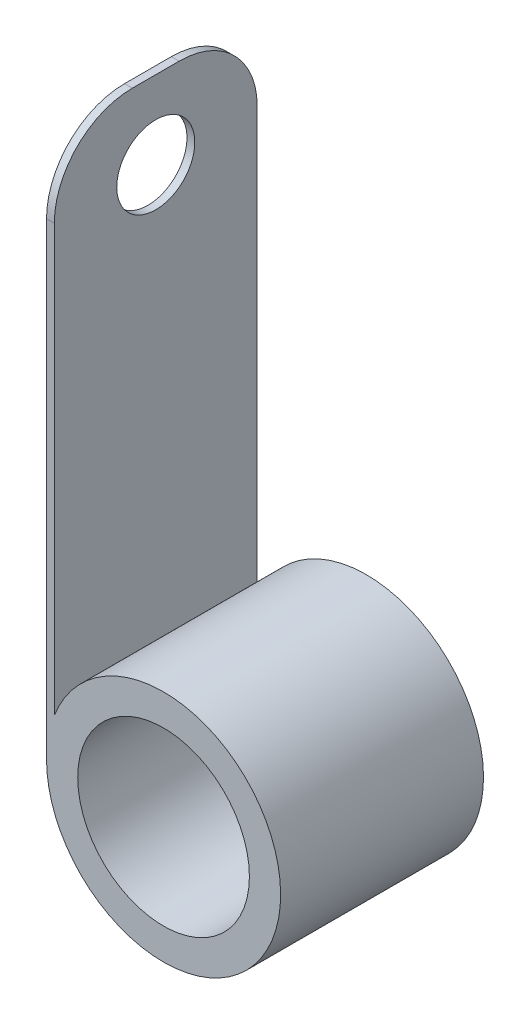
SolidWorks part; units mm, degrees
ref_plane "Plano frontal" through (0, 0, 0) normal (0, 0, 1) x (1, 0, 0)
ref_plane "Plano superior" through (0, 0, 0) normal (0, 1, 0) x (1, 0, 0)
ref_plane "Plano direito" through (0, 0, 0) normal (1, 0, 0) x (0, 0, -1)
sketch "Esboço1" plane through (0, 0, 0) normal (0, 0, 1) x (1, 0, 0)
  circle A0 centre (0, 0) radius 7.5
  circle A1 centre (0, 0) radius 5.5
  point P4 (5.5, 0)
  point P5 (7.5, 0)
  dimension "D1" = 15
  dimension "D2" = 2
extrude "Ressalto-extrusão1" add sketch "Esboço1" along normal blind 13
sketch "Esboço2" plane through (0, 0, 0) normal (0, 1, 0) x (1, 0, 0)
  line L0 (-7.5, -13) -> (7.5, -13) construction
  line L1 (-7.5, 0) -> (-7, 0)
  line L2 (-7.5, 0) -> (-7.5, -13)
  line L3 (-7.5, -13) -> (-7, -13)
  line L4 (-7, 0) -> (-7, -13)
  dimension "D1" = 0.5
extrude "Ressalto-extrusão2" add sketch "Esboço2" along normal blind 35
sketch "Esboço3" plane through (-7.5, 0, 0) normal (-1, 0, 0) x (0, 0, 1)
  line L0 (0, 35) -> (13, 35) construction
  circle A0 centre (6.5, 30) radius 2.5
  point P2 (6.5, 35)
  dimension "D1" = 5
  dimension "D2" = 5
extrude "Corte-extrusão1" cut sketch "Esboço3" against normal blind 20
fillet "Filete1" radius 5 2 edges at (-7.25, 35, 0) (-7.25, 35, 13)
